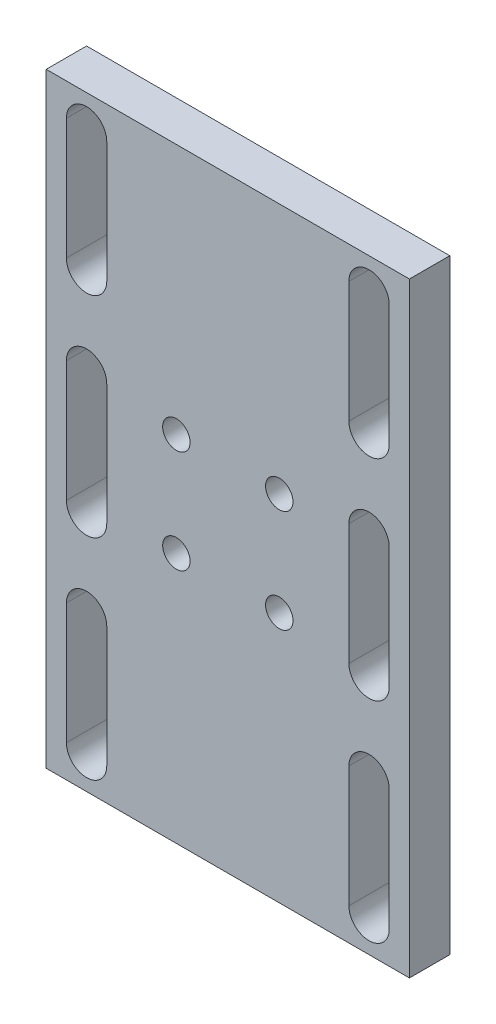
SolidWorks part; units mm, degrees
ref_plane "前基準面" through (0, 0, 0) normal (0, 0, 1) x (1, 0, 0)
ref_plane "上基準面" through (0, 0, 0) normal (0, 1, 0) x (1, 0, 0)
ref_plane "右基準面" through (0, 0, 0) normal (1, 0, 0) x (0, 0, -1)
sketch "草圖2" plane through (0, 0, 0) normal (0, 0, 1) x (1, 0, 0)
  line L0 (35, 142) -> (35, 112) construction
  line L1 (45, 150) -> (45, 0)
  line L2 (-45, 150) -> (-45, 0)
  line L3 (-45, 75) -> (-35, 75) construction
  line L4 (-35, 127) -> (-23.75, 127) construction
  line L5 (-35, 23) -> (-23.75, 23) construction
  line L8 (40, 142) -> (40, 112)
  line L9 (30, 142) -> (30, 112)
  line L10 (35, 142) -> (35, 147) construction
  line L11 (23.75, 139.5) -> (23.75, 114.5) construction
  line L12 (27, 139.5) -> (27, 114.5)
  line L13 (20.5, 139.5) -> (20.5, 114.5)
  line L15 (0, 0) -> (0, 150) construction
  line L17 (-35, 142) -> (-35, 112) construction
  line L18 (-40, 142) -> (-40, 112)
  line L19 (-30, 142) -> (-30, 112)
  line L20 (-23.75, 139.5) -> (-23.75, 114.5) construction
  line L21 (-27, 139.5) -> (-27, 114.5)
  line L22 (-20.5, 139.5) -> (-20.5, 114.5)
  line L23 (35, 60) -> (35, 90) construction
  line L24 (40, 60) -> (40, 90)
  line L25 (30, 60) -> (30, 90)
  line L26 (23.75, 62.5) -> (23.75, 87.5) construction
  line L27 (27, 62.5) -> (27, 87.5)
  line L28 (20.5, 62.5) -> (20.5, 87.5)
  line L29 (-35, 60) -> (-35, 90) construction
  line L30 (-40, 60) -> (-40, 90)
  line L31 (-30, 60) -> (-30, 90)
  line L32 (-23.75, 62.5) -> (-23.75, 87.5) construction
  line L33 (-27, 62.5) -> (-27, 87.5)
  line L34 (-20.5, 62.5) -> (-20.5, 87.5)
  line L37 (-45, 150) -> (45, 150)
  line L38 (-35, 8) -> (-35, 38) construction
  line L39 (-40, 8) -> (-40, 38)
  line L40 (-30, 8) -> (-30, 38)
  line L41 (-23.75, 10.5) -> (-23.75, 35.5) construction
  line L42 (-27, 10.5) -> (-27, 35.5)
  line L43 (-20.5, 10.5) -> (-20.5, 35.5)
  line L44 (35, 8) -> (35, 38) construction
  line L45 (40, 8) -> (40, 38)
  line L46 (30, 8) -> (30, 38)
  line L47 (23.75, 10.5) -> (23.75, 35.5) construction
  line L48 (27, 10.5) -> (27, 35.5)
  line L49 (20.5, 10.5) -> (20.5, 35.5)
  line L51 (-45, 0) -> (45, 0)
  arc A0 (40, 142) -> (30, 142) centre (35, 142) ccw
  arc A1 (30, 112) -> (40, 112) centre (35, 112) ccw
  arc A2 (27, 139.5) -> (20.5, 139.5) centre (23.75, 139.5) ccw
  arc A3 (20.5, 114.5) -> (27, 114.5) centre (23.75, 114.5) ccw
  arc A4 (-40, 142) -> (-30, 142) centre (-35, 142) cw
  arc A5 (-30, 112) -> (-40, 112) centre (-35, 112) cw
  arc A6 (-27, 139.5) -> (-20.5, 139.5) centre (-23.75, 139.5) cw
  arc A7 (-20.5, 114.5) -> (-27, 114.5) centre (-23.75, 114.5) cw
  arc A8 (40, 60) -> (30, 60) centre (35, 60) cw
  arc A9 (30, 90) -> (40, 90) centre (35, 90) cw
  arc A10 (27, 62.5) -> (20.5, 62.5) centre (23.75, 62.5) cw
  arc A11 (20.5, 87.5) -> (27, 87.5) centre (23.75, 87.5) cw
  arc A12 (-40, 60) -> (-30, 60) centre (-35, 60) ccw
  arc A13 (-30, 90) -> (-40, 90) centre (-35, 90) ccw
  arc A14 (-27, 62.5) -> (-20.5, 62.5) centre (-23.75, 62.5) ccw
  arc A15 (-20.5, 87.5) -> (-27, 87.5) centre (-23.75, 87.5) ccw
  arc A16 (-40, 8) -> (-30, 8) centre (-35, 8) ccw
  arc A17 (-30, 38) -> (-40, 38) centre (-35, 38) ccw
  arc A18 (-27, 10.5) -> (-20.5, 10.5) centre (-23.75, 10.5) ccw
  arc A19 (-20.5, 35.5) -> (-27, 35.5) centre (-23.75, 35.5) ccw
  arc A20 (40, 8) -> (30, 8) centre (35, 8) cw
  arc A21 (30, 38) -> (40, 38) centre (35, 38) cw
  arc A22 (27, 10.5) -> (20.5, 10.5) centre (23.75, 10.5) cw
  arc A23 (20.5, 35.5) -> (27, 35.5) centre (23.75, 35.5) cw
  point P8 (35, 127)
  point P17 (23.75, 127)
  point P30 (-35, 127)
  point P37 (-23.75, 127)
  point P44 (35, 75)
  point P51 (23.75, 75)
  point P58 (-35, 75)
  point P65 (-23.75, 75)
  point P77 (-35, 23)
  point P84 (-23.75, 23)
  point P91 (35, 23)
  point P98 (23.75, 23)
  dimension "D7" = 3
  dimension "D1" = 90
  dimension "D2" = 47.5
  dimension "D3" = 70
  dimension "D4" = 150
  dimension "D5" = 30
  dimension "D6" = 25
  dimension "D8" = 3
  dimension "D9" = 10
  dimension "D10" = 6.5
extrude "填料-伸長1" add sketch "草圖2" along normal blind 10 contours L2 L51 L1 L37 L46 A21 L45 A20 A19 L43 A18 L42 A17 L40 A16 L39 A15 L34 A14 L33 A13 L31 A12 L30 L25 A9 L24 A8 L19 A5 L18 A4 A3 L13 A2 L12 A1 L9
sketch "草圖3" plane through (0, 0, 10) normal (0, 0, 1) x (1, 0, 0)
  line L1 (-29.0568, 145.6979) -> (28.7653, 145.6979)
  line L2 (-29.0568, 145.6979) -> (-29.0568, 2.8892)
  line L3 (-29.0568, 2.8892) -> (28.7653, 2.8892)
  line L4 (28.7653, 145.6979) -> (28.7653, 2.8892)
extrude "填料-伸長2" add sketch "草圖3" against normal up to surface (10 mm away) up to face at (35, 23, 0)
sketch "草圖5" [suppressed] plane through (0, 0, 0) normal (0, 0, -1) x (-1, 0, 0)
  line L0 (35, 142) -> (35, 112)
  line L1 (35, 90) -> (35, 60)
  line L2 (35, 38) -> (35, 8)
  line L3 (23.75, 35.5) -> (23.75, 10.5)
  line L4 (23.75, 87.5) -> (23.75, 62.5)
  line L5 (23.75, 114.5) -> (23.75, 139.5)
  line L6 (0, 66.0858) -> (0, -47.8776) construction
  line L7 (-23.75, 114.5) -> (-23.75, 139.5)
  line L8 (-23.75, 87.5) -> (-23.75, 62.5)
  line L9 (-23.75, 35.5) -> (-23.75, 10.5)
  line L10 (-35, 38) -> (-35, 8)
  line L11 (-35, 90) -> (-35, 60)
  line L12 (-35, 142) -> (-35, 112)
sketch "草圖7" [suppressed] plane through (0, 0, 10) normal (0, 0, 1) x (1, 0, 0)
  line L0 (23.75, 114.5) -> (23.75, 139.5) construction
  line L1 (35, 142) -> (35, 112) construction
  line L2 (35, 90) -> (35, 60) construction
  line L3 (23.75, 87.5) -> (23.75, 62.5) construction
  line L4 (23.75, 35.5) -> (23.75, 10.5) construction
  line L5 (35, 38) -> (35, 8) construction
  line L6 (-23.75, 35.5) -> (-23.75, 10.5) construction
  line L7 (-35, 38) -> (-35, 8) construction
  line L8 (-35, 90) -> (-35, 60) construction
  line L9 (-23.75, 87.5) -> (-23.75, 62.5) construction
  line L10 (-23.75, 114.5) -> (-23.75, 139.5) construction
  line L11 (-35, 142) -> (-35, 112) construction
  line L12 (23.75, 114.5) -> (23.75, 139.5)
  line L13 (35, 142) -> (35, 112)
  line L14 (35, 90) -> (35, 60)
  line L15 (23.75, 87.5) -> (23.75, 62.5)
  line L16 (23.75, 35.5) -> (23.75, 10.5)
  line L17 (35, 38) -> (35, 8)
  line L18 (-23.75, 35.5) -> (-23.75, 10.5)
  line L19 (-35, 38) -> (-35, 8)
  line L20 (-35, 90) -> (-35, 60)
  line L21 (-23.75, 87.5) -> (-23.75, 62.5)
  line L22 (-23.75, 114.5) -> (-23.75, 139.5)
  line L23 (-35, 142) -> (-35, 112)
sketch "草圖8" plane through (0, 0, 10) normal (0, 0, 1) x (1, 0, 0)
  line L0 (35, 142) -> (35, 112)
  line L1 (0, 0) -> (0, -33.4877) construction
  line L2 (35, 90) -> (35, 60)
  line L3 (35, 38) -> (35, 8)
  line L4 (-35, 38) -> (-35, 8)
  line L5 (-35, 90) -> (-35, 60)
  line L6 (-35, 142) -> (-35, 112)
sketch "草圖9" plane through (0, 0, 0) normal (0, 0, -1) x (-1, 0, 0)
  line L0 (35, 142) -> (35, 112) construction
  line L1 (35, 90) -> (35, 60) construction
  line L2 (35, 38) -> (35, 8) construction
  line L3 (-35, 38) -> (-35, 8) construction
  line L4 (-35, 90) -> (-35, 60) construction
  line L5 (-35, 142) -> (-35, 112) construction
  line L6 (35, 142) -> (35, 112)
  line L7 (35, 90) -> (35, 60)
  line L8 (35, 38) -> (35, 8)
  line L9 (-35, 38) -> (-35, 8)
  line L10 (-35, 90) -> (-35, 60)
  line L11 (-35, 142) -> (-35, 112)
sketch "草圖10" plane through (0, 0, 10) normal (0, 0, 1) x (1, 0, 0)
  line L0 (72.2327, 75) -> (-114.5908, 75) construction
  line L1 (0, 0) -> (0, 138.4378) construction
  line L3 (-45, 0) -> (45, 0) construction
  circle A0 centre (12.75, 62.25) radius 3.4
  circle A1 centre (-12.75, 62.25) radius 3.4
  circle A2 centre (12.75, 87.75) radius 3.4
  circle A3 centre (-12.75, 87.75) radius 3.4
  dimension "D2" = 6.8
  dimension "D1" = 75
  dimension "D3" = 25.5
  dimension "D4" = 25.5
extrude "除料-伸長1" cut sketch "草圖10" against normal up to next
